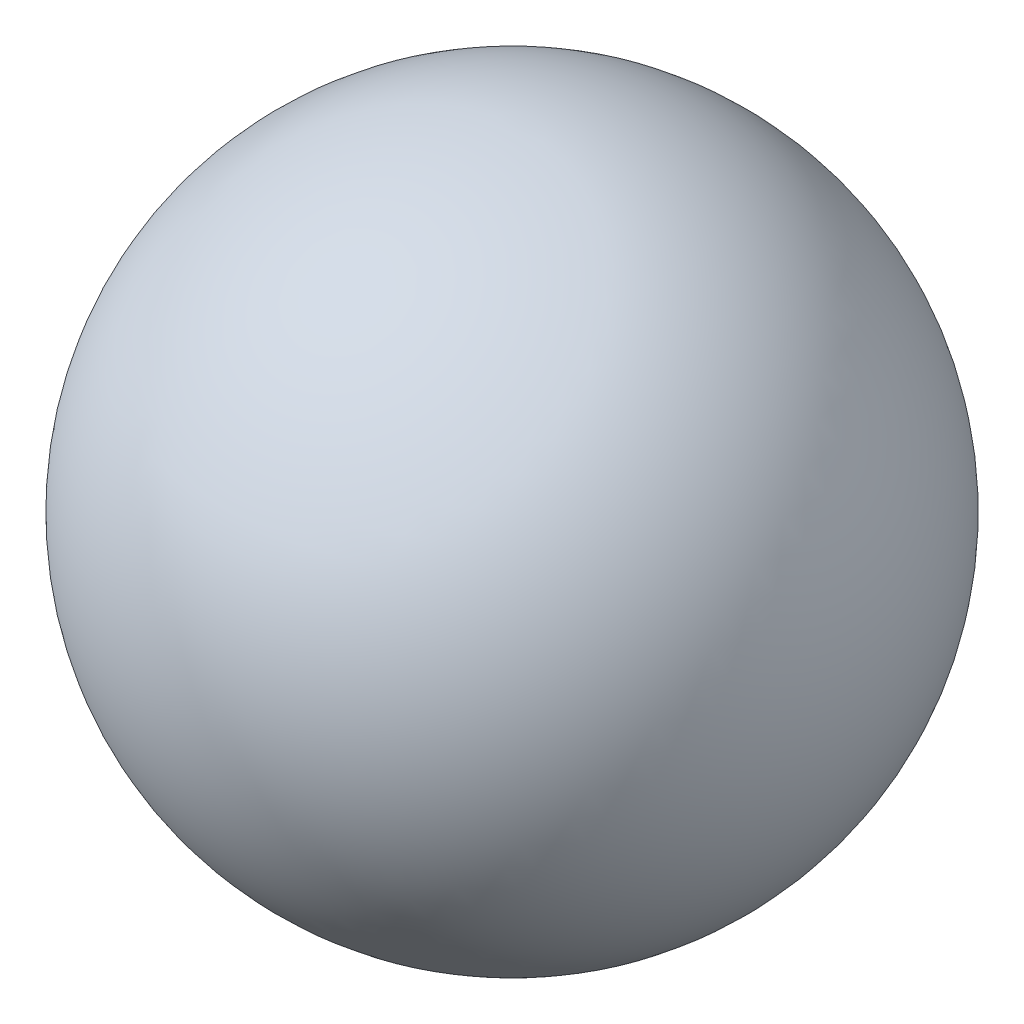
SolidWorks part; units mm, degrees
ref_plane "Front Plane" through (0, 0, 0) normal (0, 0, 1) x (1, 0, 0)
ref_plane "Top Plane" through (0, 0, 0) normal (0, 1, 0) x (1, 0, 0)
ref_plane "Right Plane" through (0, 0, 0) normal (1, 0, 0) x (0, 0, -1)
sketch "Sketch1" plane through (0, 0, 0) normal (0, 0, 1) x (1, 0, 0)
  line L0 (0, 105.0842) -> (0, -101.9811) construction
  line L1 (0, 21.5) -> (0, 16.75)
  line L2 (0, -16.75) -> (0, -21.5)
  line L3 (0, 16.75) -> (0, -16.75)
  arc A0 (0, 21.5) -> (0, -21.5) centre (0, 0) ccw
  dimension "D1" = 21.5
revolve "Revolve1" add sketch "Sketch1" angle 360 about L0
